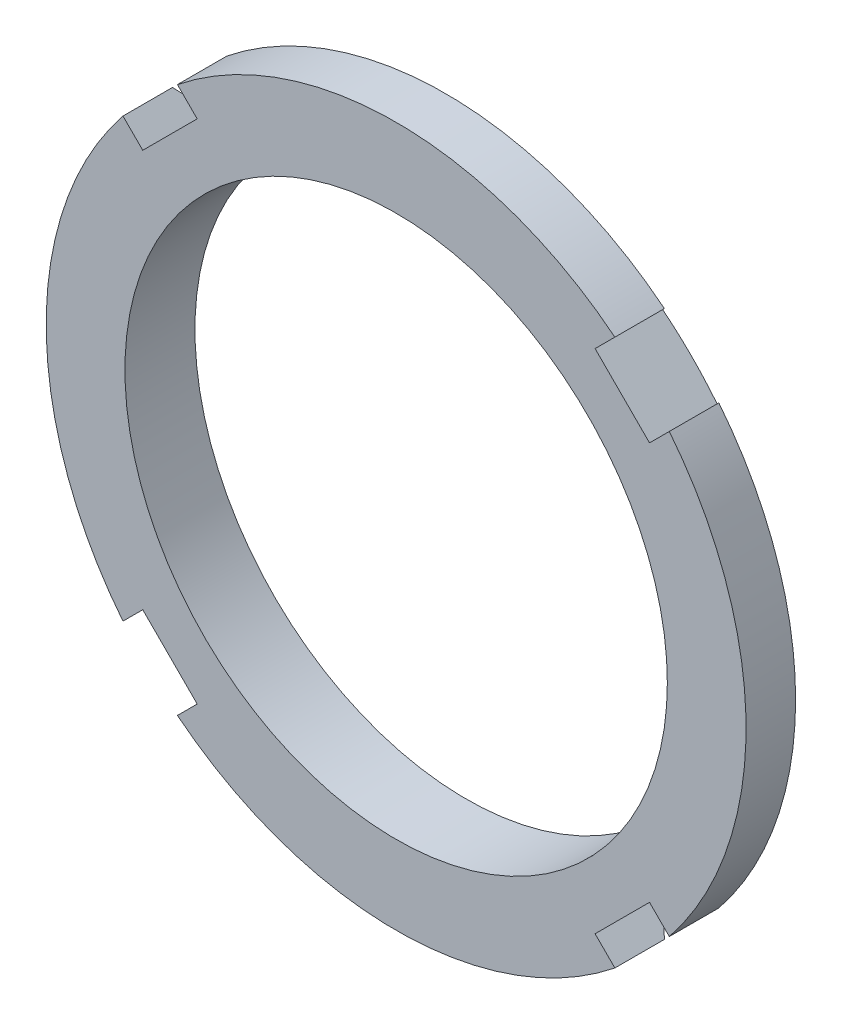
SolidWorks part; units mm, degrees
material "Alloy Steel"
ref_plane "Front Plane" through (0, 0, 0) normal (0, 0, 1) x (1, 0, 0)
ref_plane "Top Plane" through (0, 0, 0) normal (0, 1, 0) x (1, 0, 0)
ref_plane "Right Plane" through (0, 0, 0) normal (1, 0, 0) x (0, 0, -1)
sketch "Sketch1" plane through (0, 0, 0) normal (0, 0, 1) x (1, 0, 0)
  circle A0 centre (0, 0) radius 50
  circle A1 centre (0, 0) radius 38.75
  dimension "D1" = 100
  dimension "D2" = 77.5
extrude "Extrude1" add sketch "Sketch1" along normal blind 10
sketch "Sketch2" plane through (0, 0, 10) normal (0, 0, 1) x (1, 0, 0)
  line L0 (0, 0) -> (22.7176, 0) construction
  line L1 (0, 0) -> (15.6425, 15.6425) construction
  line L2 (31.2517, 39.0299) -> (28.4257, 36.2039)
  line L3 (28.4257, 36.2039) -> (36.2039, 28.4257)
  line L4 (39.0299, 31.2517) -> (36.2039, 28.4257)
  arc A1 (39.0299, 31.2517) -> (31.2517, 39.0299) centre (0, 0) ccw
  circle A3 centre (0, 0) radius 50 construction
  dimension "D3" = 45.7
  dimension "D1" = 45
  dimension "D2" = 11
extrude "Cut-Extrude1" cut sketch "Sketch2" against normal through all
pattern_circular "CirPattern1" count 4 over 360 about axis through (0, 0, 0) along (0, 0, 1) of "Cut-Extrude1"
sketch "Sketch3" plane through (0, 0, 0) normal (0, 1, 0) x (1, 0, 0)
  line L0 (50, 0) -> (39.0299, 0) construction
  line L1 (50, -10) -> (50, 0) construction
  line L2 (50, 0) -> (45.5, 0)
  line L3 (50, -2.9223) -> (50, 0)
  line L4 (45.5, 0) -> (50, -2.9223)
  line L5 (0, 0) -> (0, 7.6185) construction
  dimension "D1" = 91
  dimension "D2" = 33
revolve "Cut-Revolve1" cut sketch "Sketch3" angle 360 about L5
